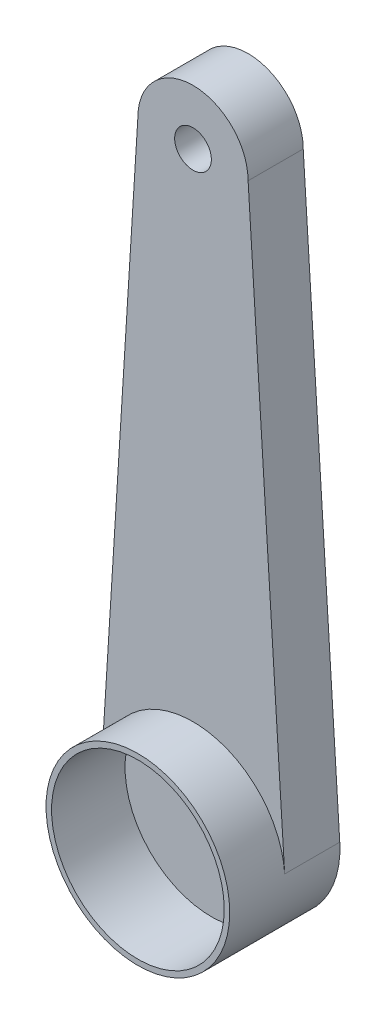
SolidWorks part; units mm, degrees
ref_plane "Front Plane" through (0, 0, 0) normal (0, 0, 1) x (1, 0, 0)
ref_plane "Top Plane" through (0, 0, 0) normal (0, 1, 0) x (1, 0, 0)
ref_plane "Right Plane" through (0, 0, 0) normal (1, 0, 0) x (0, 0, -1)
sketch "Sketch1" plane through (0, 0, 0) normal (0, 0, 1) x (1, 0, 0)
  line L0 (0, 0) -> (0, 16) construction
  line L1 (-1.5, 16) -> (-2.4951, 0.1567)
  line L2 (1.5, 16) -> (2.4951, 0.1567)
  arc A0 (-2.4951, 0.1567) -> (2.4951, 0.1567) centre (0, 0) ccw
  arc A1 (1.5, 16) -> (-1.5, 16) centre (0, 16) ccw
  dimension "D1" = 5
  dimension "D3" = 3
  dimension "D2" = 16
extrude "Boss-Extrude1" add sketch "Sketch1" along normal blind 1.5
sketch "Sketch2" plane through (0, 0, 1.5) normal (0, 0, 1) x (1, 0, 0)
  circle A0 centre (0, 0) radius 2.5
extrude "Boss-Extrude2" add sketch "Sketch2" along normal blind 1.5
sketch "Sketch3" plane through (0, 0, 3) normal (0, 0, 1) x (1, 0, 0)
  circle A0 centre (0, 0) radius 2.35
  dimension "D1" = 4.7
extrude "Cut-Extrude1" cut sketch "Sketch3" against normal blind 2
sketch "Sketch4" plane through (0, 0, 1.5) normal (0, 0, 1) x (1, 0, 0)
  circle A0 centre (0, 16) radius 0.5
  dimension "D1" = 1
extrude "Cut-Extrude2" cut sketch "Sketch4" against normal blind 2
